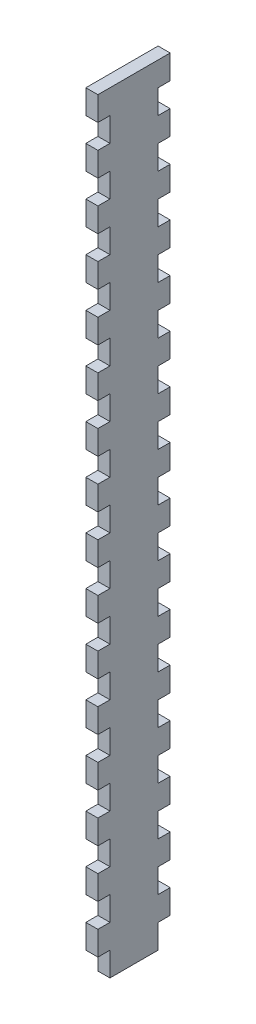
SolidWorks part; units mm, degrees
ref_plane "Front Plane" through (0, 0, 0) normal (0, 0, 1) x (1, 0, 0)
ref_plane "Top Plane" through (0, 0, 0) normal (0, 1, 0) x (1, 0, 0)
ref_plane "Right Plane" through (0, 0, 0) normal (1, 0, 0) x (0, 0, -1)
sketch "Sketch1" plane through (0, 0, 0) normal (1, 0, 0) x (0, 0, -1)
  line L1 (0, 0) -> (38.1, 0)
  line L2 (0, 0) -> (0, 406.4)
  line L3 (0, 406.4) -> (38.1, 406.4)
  line L4 (38.1, 0) -> (38.1, 406.4)
  dimension "D1" = 38.1
  dimension "D2" = 406.4
extrude "Boss-Extrude1" add sketch "Sketch1" along normal blind 6.35 contours L2 L3 L4 L1
sketch "Sketch2" plane through (6.35, 0, 0) normal (1, 0, 0) x (0, 0, -1)
  line L1 (0, 0) -> (6.35, 0)
  line L2 (0, 0) -> (0, 12.7)
  line L3 (0, 12.7) -> (6.35, 12.7)
  line L4 (6.35, 0) -> (6.35, 12.7)
  line L5 (38.1, 0) -> (31.75, 0)
  line L6 (38.1, 0) -> (38.1, 12.7)
  line L7 (38.1, 12.7) -> (31.75, 12.7)
  line L8 (31.75, 0) -> (31.75, 12.7)
  dimension "D1" = 6.35
  dimension "D2" = 12.7
extrude "Cut-Extrude1" cut sketch "Sketch2" against normal through all
pattern_linear "LPattern1" count 16 spacing 25.4 along (0, 1, 0) of "Cut-Extrude1"
